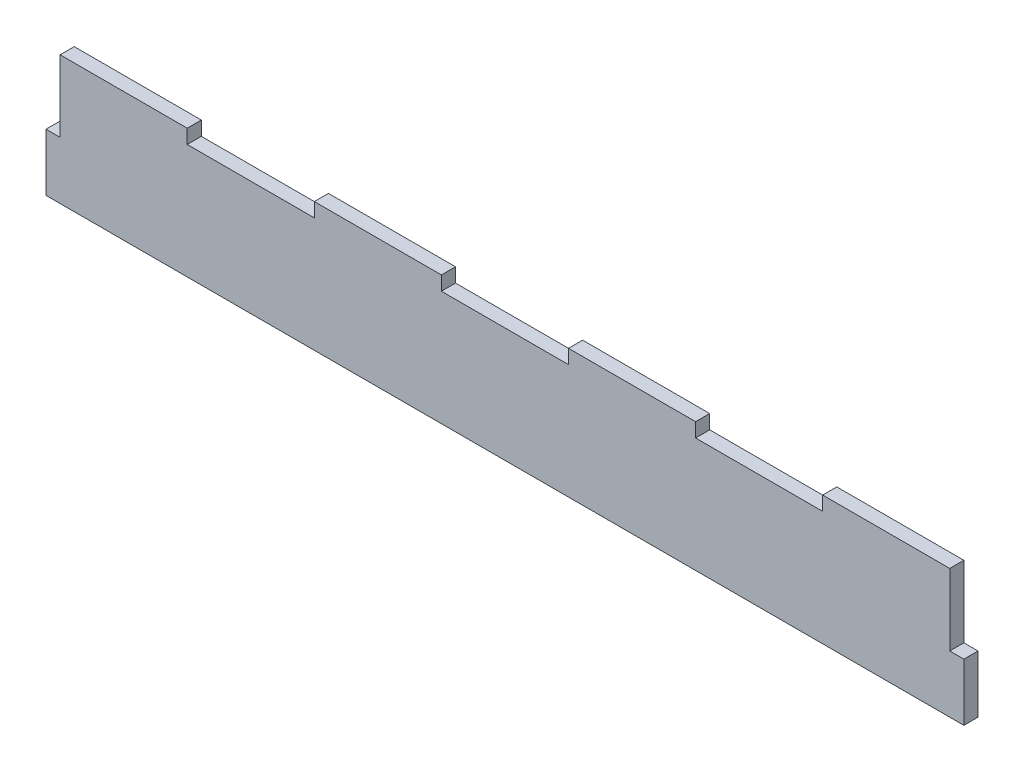
SolidWorks part; units mm, degrees
material "A-Glass Fiber"
ref_plane "Front Plane" through (0, 0, 0) normal (0, 0, 1) x (1, 0, 0)
ref_plane "Top Plane" through (0, 0, 0) normal (0, 1, 0) x (1, 0, 0)
ref_plane "Right Plane" through (0, 0, 0) normal (1, 0, 0) x (0, 0, -1)
sketch "Sketch1" plane through (0, 0, 0) normal (0, 0, 1) x (1, 0, 0)
  line L0 (101.6, -10.16) -> (10.16, -10.16)
  line L1 (0, 0) -> (660.4, 0)
  line L2 (0, 0) -> (0, -92.71)
  line L3 (0, -92.71) -> (660.4, -92.71)
  line L4 (660.4, 0) -> (660.4, -92.71)
  line L5 (0, -92.71) -> (10.16, -92.71)
  line L6 (0, -92.71) -> (0, -51.435)
  line L7 (0, -51.435) -> (10.16, -51.435)
  line L8 (10.16, -92.71) -> (10.16, -51.435)
  line L9 (0, 0) -> (660.4, 0)
  line L10 (0, 0) -> (0, -10.16)
  line L12 (660.4, 0) -> (660.4, -10.16)
  line L13 (660.4, -10.16) -> (650.24, -10.16)
  line L14 (660.4, -10.16) -> (660.4, -51.435)
  line L15 (660.4, -51.435) -> (650.24, -51.435)
  line L16 (650.24, -10.16) -> (650.24, -51.435)
  line L17 (650.24, -51.435) -> (660.4, -51.435)
  line L18 (650.24, -51.435) -> (650.24, -92.71)
  line L19 (650.24, -92.71) -> (660.4, -92.71)
  line L20 (660.4, -51.435) -> (660.4, -92.71)
  line L21 (10.16, -51.435) -> (0, -51.435)
  line L22 (10.16, -51.435) -> (10.16, -10.16)
  line L23 (10.16, -10.16) -> (0, -10.16)
  line L24 (0, -51.435) -> (0, -10.16)
  line L25 (0, 0) -> (101.6, 0)
  line L26 (0, 0) -> (0, -10.16)
  line L29 (101.6, -10.16) -> (193.04, -10.16)
  line L30 (101.6, -10.16) -> (101.6, 0)
  line L31 (101.6, 0) -> (193.04, 0)
  line L32 (193.04, -10.16) -> (193.04, 0)
  line L33 (193.04, 0) -> (284.48, 0)
  line L34 (193.04, 0) -> (193.04, -10.16)
  line L35 (193.04, -10.16) -> (284.48, -10.16)
  line L36 (284.48, 0) -> (284.48, -10.16)
  line L37 (284.48, -10.16) -> (375.92, -10.16)
  line L38 (284.48, -10.16) -> (284.48, 0)
  line L39 (284.48, 0) -> (375.92, 0)
  line L40 (375.92, -10.16) -> (375.92, 0)
  line L41 (467.36, -10.16) -> (375.92, -10.16)
  line L42 (467.36, -10.16) -> (467.36, 0)
  line L43 (467.36, 0) -> (375.92, 0)
  line L44 (375.92, -10.16) -> (375.92, 0)
  line L45 (467.36, 0) -> (558.8, 0)
  line L46 (467.36, 0) -> (467.36, -10.16)
  line L47 (467.36, -10.16) -> (558.8, -10.16)
  line L48 (558.8, 0) -> (558.8, -10.16)
  line L49 (558.8, -10.16) -> (650.24, -10.16)
  line L50 (558.8, -10.16) -> (558.8, 0)
  line L51 (558.8, 0) -> (650.24, 0)
  line L52 (650.24, -10.16) -> (650.24, 0)
  line L53 (10.16, -10.16) -> (0, -10.16)
  line L54 (10.16, -10.16) -> (10.16, 0)
  line L55 (10.16, 0) -> (0, 0)
  line L56 (0, -10.16) -> (0, 0)
  dimension "D1" = 660.4
  dimension "D2" = 92.71
  dimension "D3" = 10.16
  dimension "D4" = 10.16
  dimension "D5" = 10.16
extrude "Boss-Extrude1" add sketch "Sketch1" along normal blind 10.16 contours L49 L47 L41 L37 L35 L29 L0 L22 L8 L3 L18 L16 | L15 L18 L3 L4 | L49 L52 L1 L48 | L41 L42 L1 L40 | L36 L1 L32 L35 | L54 L0 L30 L25 | L3 L8 L7 L2
